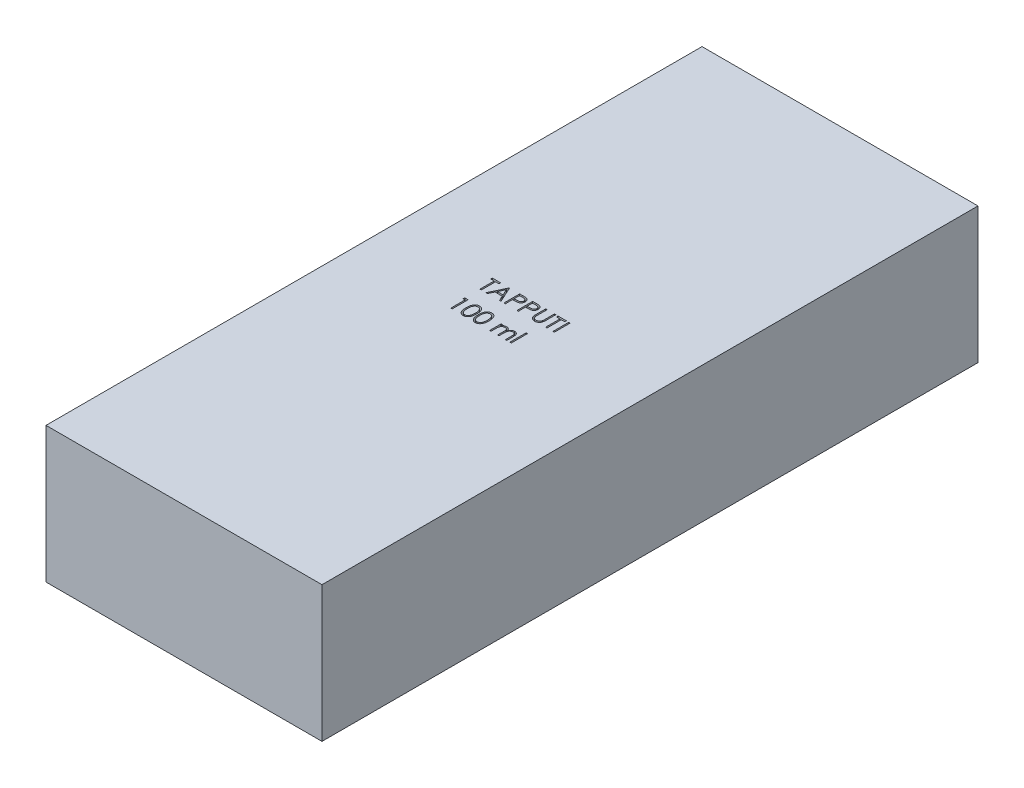
SolidWorks part; units mm, degrees
ref_plane "Front Plane" through (0, 0, 0) normal (0, 0, 1) x (1, 0, 0)
ref_plane "Top Plane" through (0, 0, 0) normal (0, 1, 0) x (1, 0, 0)
ref_plane "Right Plane" through (0, 0, 0) normal (1, 0, 0) x (0, 0, -1)
sketch "Sketch1" plane through (0, 0, 0) normal (0, 1, 0) x (1, 0, 0)
  line L1 (-30.5, 72.5) -> (30.5, 72.5)
  line L2 (-30.5, 72.5) -> (-30.5, -72.5)
  line L3 (-30.5, -72.5) -> (30.5, -72.5)
  line L4 (30.5, 72.5) -> (30.5, -72.5)
  line L5 (-30.5, 72.5) -> (30.5, -72.5) construction
  line L6 (-30.5, -72.5) -> (30.5, 72.5) construction
  point P0 (0, 0)
  dimension "D1" = 61
  dimension "D2" = 145
extrude "Boss-Extrude1" add sketch "Sketch1" against normal blind 30
sketch "Sketch2" plane through (0, 0, 0) normal (0, 1, 0) x (1, 0, 0)
  text T0 "TAPPUTI \r\n100 ml"
extrude "Cut-Extrude1" cut sketch "Sketch2" against normal blind 10
